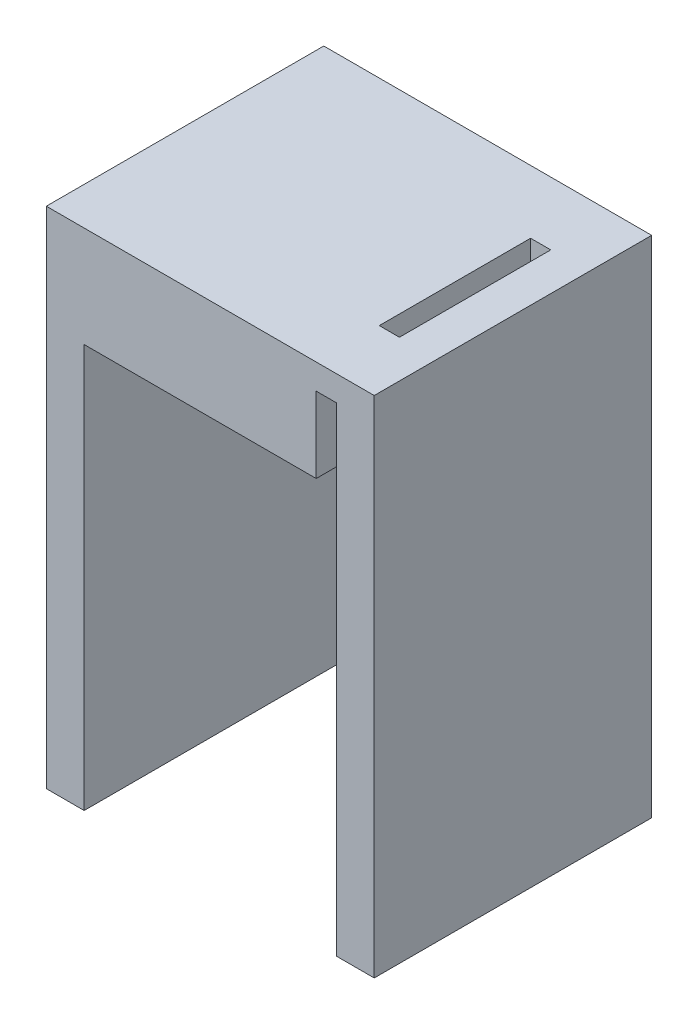
SolidWorks part; units mm, degrees
ref_plane "Front Plane" through (0, 0, 0) normal (0, 0, 1) x (1, 0, 0)
ref_plane "Top Plane" through (0, 0, 0) normal (0, 1, 0) x (1, 0, 0)
ref_plane "Right Plane" through (0, 0, 0) normal (1, 0, 0) x (0, 0, -1)
sketch "Sketch1" plane through (0, 0, 0) normal (0, 0, 1) x (1, 0, 0)
  line L0 (0, 0) -> (0, 20.32)
  line L1 (0, 20.32) -> (-12.7, 20.32)
  line L2 (-12.7, 20.32) -> (-12.7, 0)
  line L3 (-12.7, 0) -> (-14.605, 0)
  line L4 (-14.605, 0) -> (-14.605, 19.05)
  line L5 (-14.605, 19.05) -> (-14.605, 25.4)
  line L6 (-14.605, 25.4) -> (1.905, 25.4)
  line L7 (1.905, 25.4) -> (1.905, 19.05)
  line L8 (1.905, 19.05) -> (1.905, 0)
  line L9 (1.905, 0) -> (0, 0)
extrude "Boss-Extrude1" add sketch "Sketch1" against normal blind 13.97
sketch "Sketch3" plane through (0, 0, 0) normal (0, 0, 1) x (1, 0, 0)
  line L0 (0, 20.32) -> (0, 24.13)
  line L1 (-12.7, 20.32) -> (0, 20.32) construction
  line L2 (0, 24.13) -> (-1.016, 24.13)
  line L3 (0, 20.32) -> (-1.016, 20.32)
  line L4 (-1.016, 24.13) -> (-1.016, 20.32)
extrude "Cut-Extrude1" cut sketch "Sketch3" against normal through all
sketch "Sketch4" plane through (0, 24.13, 0) normal (0, -1, 0) x (1, 0, 0)
  line L0 (-1.016, -6.985) -> (-1.016, -3.175)
  line L1 (-1.016, -13.97) -> (-1.016, 0) construction
  line L2 (-1.016, -13.97) -> (-1.016, 0) construction
  line L3 (-1.016, -3.175) -> (0, -3.175)
  line L4 (0, -13.97) -> (0, 0) construction
  line L5 (0, -3.175) -> (0, -10.795)
  line L6 (0, -10.795) -> (-1.016, -10.795)
  line L7 (-1.016, -10.795) -> (-1.016, -6.985)
extrude "Cut-Extrude2" cut sketch "Sketch4" against normal through all
